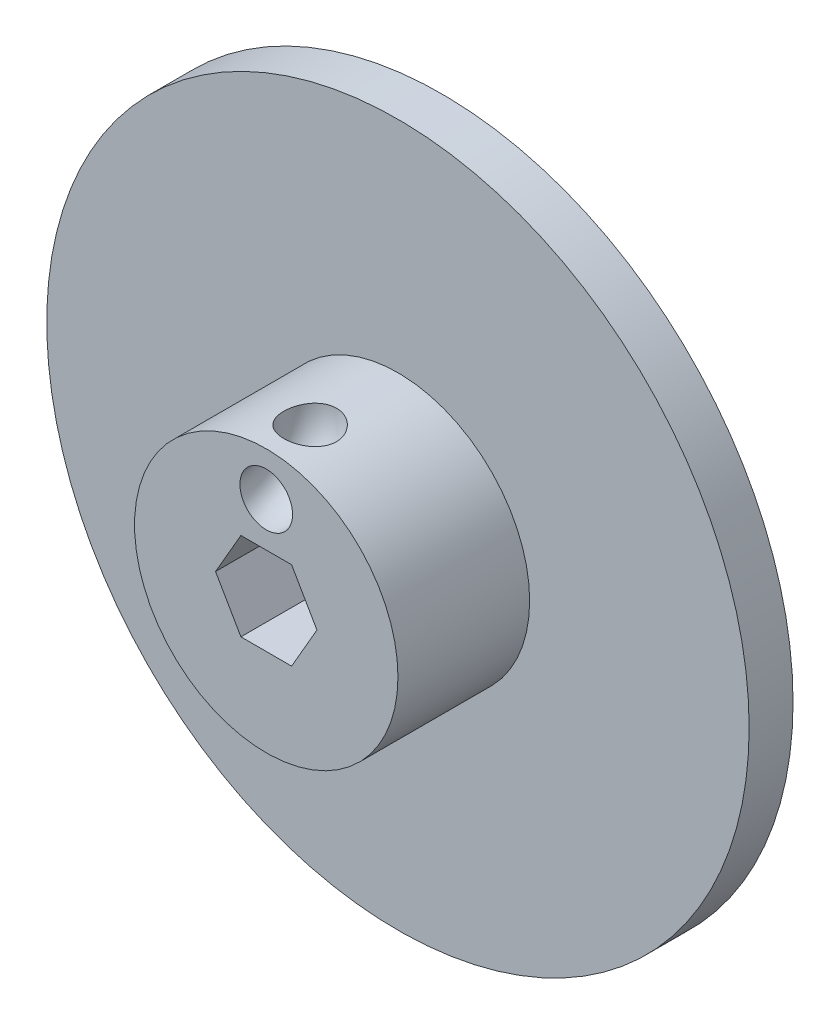
SolidWorks part; units mm, degrees
ref_plane "Front Plane" through (0, 0, 0) normal (0, 0, 1) x (1, 0, 0)
ref_plane "Top Plane" through (0, 0, 0) normal (0, 1, 0) x (1, 0, 0)
ref_plane "Right Plane" through (0, 0, 0) normal (1, 0, 0) x (0, 0, -1)
sketch "Sketch1" plane through (0, 0, 0) normal (0, 0, 1) x (1, 0, 0)
  circle A0 centre (0, 0) radius 50.8
  dimension "D1" = 101.6
extrude "Boss-Extrude1" add sketch "Sketch1" along normal blind 6.35
sketch "Sketch2" plane through (0, 0, 6.35) normal (0, 0, 1) x (1, 0, 0)
  circle A0 centre (0, 0) radius 19.05
  dimension "D1" = 38.1
extrude "Boss-Extrude2" add sketch "Sketch2" along normal blind 19.05
sketch "Sketch3" plane through (0, 0, 25.4) normal (0, 0, 1) x (1, 0, 0)
  line L0 (0, 0) -> (0, 6.35)
  line L1 (7.3323, 0) -> (3.6662, 6.35)
  line L2 (3.6662, 6.35) -> (-3.6662, 6.35)
  line L3 (-3.6662, 6.35) -> (-7.3323, 0)
  line L4 (-7.3323, 0) -> (-3.6662, -6.35)
  line L5 (-3.6662, -6.35) -> (3.6662, -6.35)
  line L6 (3.6662, -6.35) -> (7.3323, 0)
  circle A0 centre (0, 0) radius 6.35 construction
extrude "Cut-Extrude1" cut sketch "Sketch3" against normal up to surface (25.4 mm away) up to face at (50.8, 0, 0)
ref_plane "Plane1" through (0, 19.05, 0) normal (0, 1, 0) x (1, 0, 0)
sketch "Sketch4" plane through (0, 19.05, 0) normal (0, 1, 0) x (1, 0, 0)
  line L0 (0, -25.4) -> (0, -19.05)
  line L1 (3.6662, -25.4) -> (-3.6662, -25.4) construction
  line L2 (25.4, -25.4) -> (-25.4, -25.4)
  circle A0 centre (0, -19.05) radius 3.81
  point P9 (0, -25.4)
  dimension "D1" = 25.4
revolve "Cut-Revolve1" cut sketch "Sketch4" about L2
